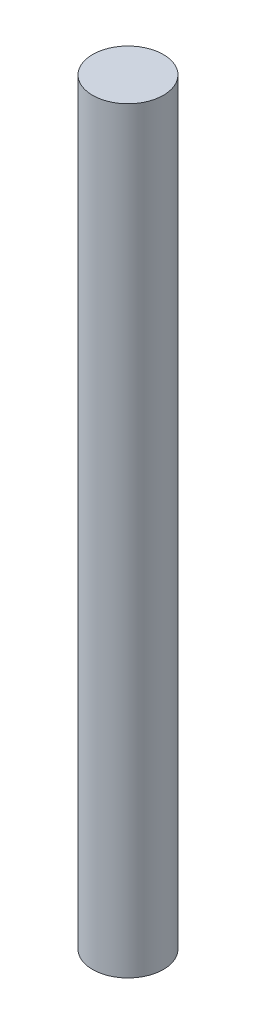
SolidWorks part; units mm, degrees
ref_plane "Front Plane" through (0, 0, 0) normal (0, 0, 1) x (1, 0, 0)
ref_plane "Top Plane" through (0, 0, 0) normal (0, 1, 0) x (1, 0, 0)
ref_plane "Right Plane" through (0, 0, 0) normal (1, 0, 0) x (0, 0, -1)
sketch "Sketch1" plane through (0, 0, 0) normal (0, 1, 0) x (1, 0, 0)
  circle A0 centre (0, 0) radius 2.5
  dimension "D1" = 5
extrude "Boss-Extrude1" add sketch "Sketch1" along normal blind 53.5
